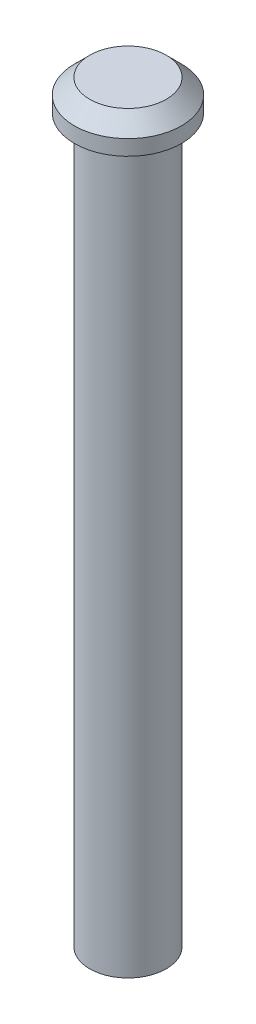
SolidWorks part; units mm, degrees
ref_plane "Front Plane" through (0, 0, 0) normal (0, 0, 1) x (1, 0, 0)
ref_plane "Top Plane" through (0, 0, 0) normal (0, 1, 0) x (1, 0, 0)
ref_plane "Right Plane" through (0, 0, 0) normal (1, 0, 0) x (0, 0, -1)
sketch "Sketch1" plane through (0, 0, 0) normal (0, 1, 0) x (1, 0, 0)
  circle A0 centre (0, 0) radius 2.5
  dimension "D1" = 5
extrude "Boss-Extrude1" add sketch "Sketch1" along normal blind 47.2
sketch "Sketch2" plane through (0, 47.2, 0) normal (0, 1, 0) x (1, 0, 0)
  circle A0 centre (0, 0) radius 3.5
  dimension "D1" = 7
extrude "Boss-Extrude2" add sketch "Sketch2" along normal blind 2
chamfer "Chamfer1" distance 1 angle 45 1 edges at (0, 49.2, 3.5)
sketch "Sketch3" plane through (0, 0, 0) normal (0, -1, 0) x (1, 0, 0)
  circle A0 centre (0, 0) radius 1.5
  dimension "D1" = 3
extrude "Cut-Extrude1" cut sketch "Sketch3" against normal blind 5
